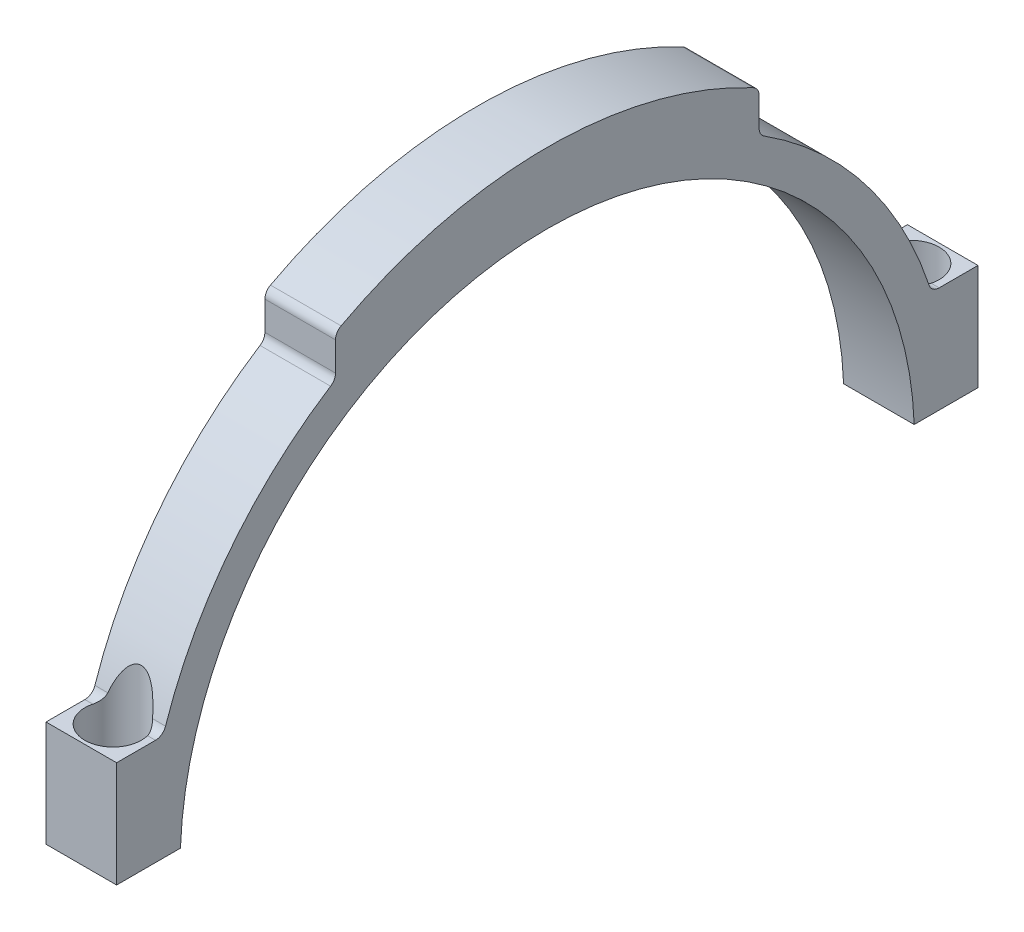
SolidWorks part; units mm, degrees
material "1060 Alloy"
ref_plane "Front Plane" through (0, 0, 0) normal (0, 0, 1) x (1, 0, 0)
ref_plane "Top Plane" through (0, 0, 0) normal (0, 1, 0) x (1, 0, 0)
ref_plane "Right Plane" through (0, 0, 0) normal (1, 0, 0) x (0, 0, -1)
sketch "Sketch1" plane through (0, 0, 0) normal (1, 0, 0) x (0, 0, -1)
  line L0 (-30, 53.3667) -> (-30, 49.295)
  line L1 (30, 53.3667) -> (30, 49.295)
  line L2 (-61.0015, 2) -> (-51.9615, 2)
  line L3 (51.9615, 2) -> (60.9985, 2)
  line L4 (-61.0015, 2) -> (-61.0015, 17)
  line L5 (-61.0015, 17) -> (-55.4977, 17)
  line L6 (60.9985, 2) -> (60.9985, 17)
  line L7 (60.9985, 17) -> (55.4977, 17)
  arc A0 (51.9615, 2) -> (-51.9615, 2) centre (0, 0) ccw
  arc A1 (54.0747, 18.0256) -> (30.6923, 48.0311) centre (0, 0) ccw
  circle A2 centre (0, 0) radius 57 construction
  circle A3 centre (0, 0) radius 52 construction
  arc A4 (29.2066, 54.6898) -> (-29.2066, 54.6898) centre (0, 0) ccw
  arc A5 (55.4977, 17) -> (54.0747, 18.0256) centre (55.4977, 18.5) cw
  arc A6 (58.8181, 19.6068) -> (-58.8181, 19.6068) centre (0, 0) ccw construction
  arc A7 (-55.4977, 17) -> (-54.0747, 18.0256) centre (-55.4977, 18.5) ccw
  arc A8 (-30.6923, 48.0311) -> (-54.0747, 18.0256) centre (0, 0) ccw
  arc A9 (54.0747, 18.0256) -> (-54.0747, 18.0256) centre (0, 0) ccw construction
  arc A10 (30.6923, 48.0311) -> (30, 49.295) centre (31.5, 49.295) cw
  arc A11 (30, 53.3667) -> (29.2066, 54.6898) centre (28.5, 53.3667) ccw
  arc A12 (-30, 53.3667) -> (-29.2066, 54.6898) centre (-28.5, 53.3667) cw
  arc A13 (-30.6923, 48.0311) -> (-30, 49.295) centre (-31.5, 49.295) ccw
  dimension "D1" = 104
  dimension "D2" = 5
  dimension "D6" = 1.5
  dimension "D3" = 30
  dimension "D4" = 30
  dimension "D7" = 122
  dimension "D8" = 9.04
  dimension "D5" = 5
extrude "Boss-Extrude1" add sketch "Sketch1" along normal blind 10
hole_wizard "M4 Tapped Hole1" positions "Sketch5" profile "Sketch4" tap size "M4" standard "ISO"
sketch "Sketch5" plane through (0, 17, 0) normal (0, 1, 0) x (1, 0, 0)
  line L0 (10, 60.9985) -> (10, 55.4977) construction
  line L1 (10, -61.0015) -> (0, -61.0015) construction
  line L2 (10, 60.9985) -> (0, 60.9985) construction
  line L4 (10, -55.4977) -> (10, -61.0015) construction
  point P0 (5, 56.4985)
  point P11 (5, -56.5015)
  dimension "D1" = 5
  dimension "D2" = 4.5
  dimension "D3" = 4.5
  dimension "D4" = 5
sketch "Sketch4" plane through (5, 17, -56.4985) normal (1, 0, 0) x (0, 0, 1)
  line L0 (0, 0) -> (0, 21.0914)
  line L1 (0, 21.0914) -> (1.65, 20.1)
  line L2 (1.65, 20.1) -> (1.65, 0)
  line L5 (1.65, 0) -> (0, 0)
  line L10 (0, 21.0914) -> (-1.65, 20.1) construction
  line L11 (0, -6.35) -> (0, 107.95) construction
  dimension "Tap Drill Dia." = 3.3
  dimension "Tap Drill Depth" = 20.1
  dimension "Drill Angle" = 118
cosmetic thread "Hole Thread3" parameters "D1"=8, "D2"=4
cosmetic thread "Hole Thread4" parameters "D1"=8, "D2"=4
sketch "Sketch7" plane through (0, 17, 0) normal (0, 1, 0) x (1, 0, 0)
  circle A0 centre (5, 56.4985) radius 4
  circle A1 centre (5, -56.5015) radius 4
  dimension "D1" = 8
extrude "Cut-Extrude1" cut sketch "Sketch7" against normal blind 6.6 and the other way blind 10
